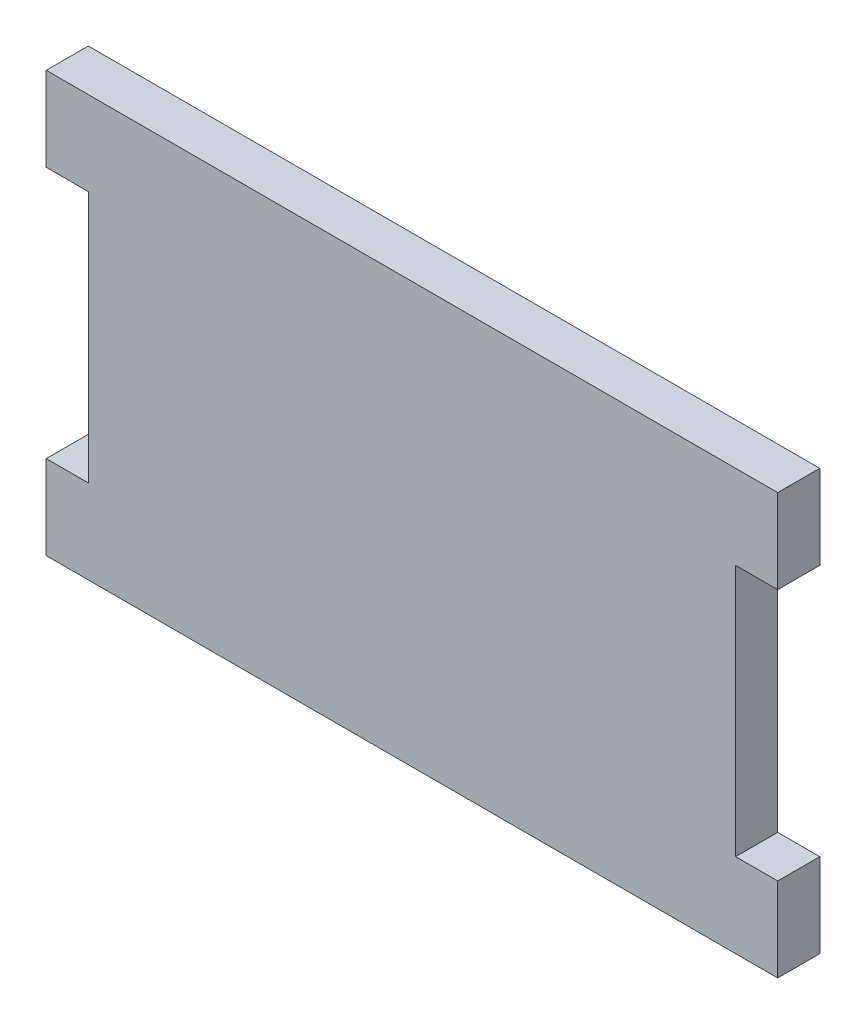
SolidWorks part; units mm, degrees
ref_plane "Front Plane" through (0, 0, 0) normal (0, 0, 1) x (1, 0, 0)
ref_plane "Top Plane" through (0, 0, 0) normal (0, 1, 0) x (1, 0, 0)
ref_plane "Right Plane" through (0, 0, 0) normal (1, 0, 0) x (0, 0, -1)
sketch "Sketch1" plane through (0, 0, 0) normal (0, 0, 1) x (1, 0, 0)
  line L0 (43.5, -15) -> (43.5, -25)
  line L1 (-43.5, 25) -> (43.5, 25)
  line L2 (-43.5, 25) -> (-43.5, 15)
  line L3 (-43.5, -25) -> (43.5, -25)
  line L4 (43.5, 25) -> (43.5, 15)
  line L5 (-43.5, 25) -> (43.5, -25) construction
  line L6 (-43.5, -25) -> (43.5, 25) construction
  line L7 (43.5, 15) -> (38.5, 15)
  line L9 (43.5, -15) -> (38.5, -15)
  line L10 (38.5, 15) -> (38.5, -15)
  line L11 (-43.5, 15) -> (-38.5, 15)
  line L13 (-43.5, -15) -> (-38.5, -15)
  line L14 (-38.5, 15) -> (-38.5, -15)
  line L15 (-43.5, -15) -> (-43.5, -25)
  point P0 (0, 0)
  dimension "D1" = 87
  dimension "D2" = 50
  dimension "D3" = 10
  dimension "D4" = 10
  dimension "D5" = 10
  dimension "D6" = 10
  dimension "D7" = 5
  dimension "D8" = 5
extrude "Boss-Extrude1" add sketch "Sketch1" along normal blind 5
